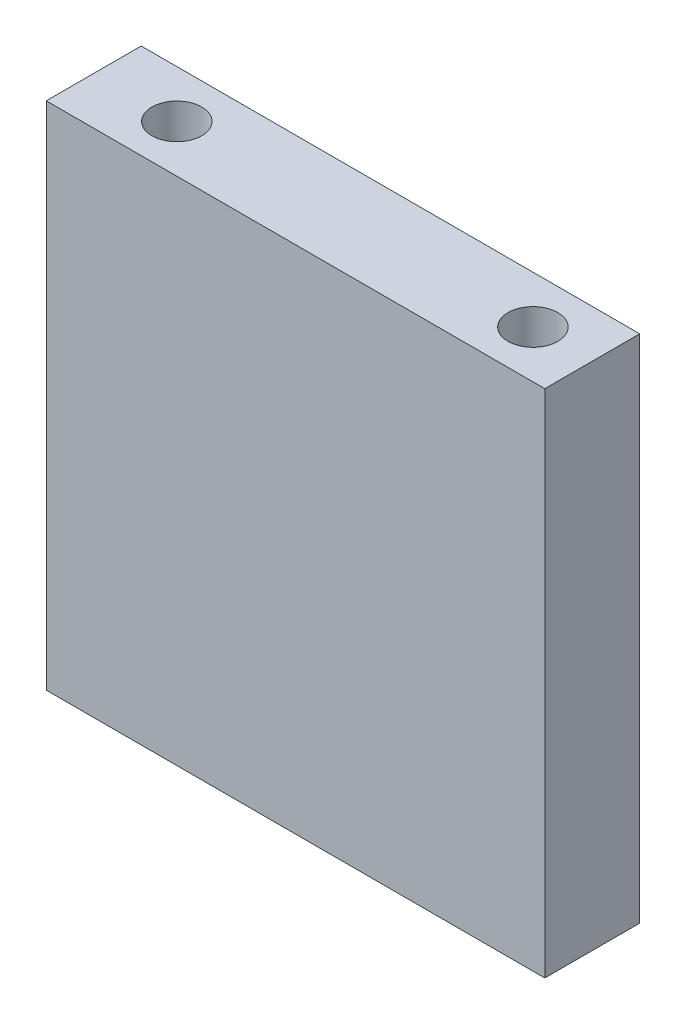
SolidWorks part; units mm, degrees
ref_plane "Front Plane" through (0, 0, 0) normal (0, 0, 1) x (1, 0, 0)
ref_plane "Top Plane" through (0, 0, 0) normal (0, 1, 0) x (1, 0, 0)
ref_plane "Right Plane" through (0, 0, 0) normal (1, 0, 0) x (0, 0, -1)
sketch "Sketch1" plane through (0, 0, 0) normal (0, 0, 1) x (1, 0, 0)
  line L1 (0, 0) -> (42, 0)
  line L2 (0, 0) -> (0, 43)
  line L3 (0, 43) -> (42, 43)
  line L4 (42, 0) -> (42, 43)
  dimension "D1" = 43
  dimension "D2" = 42
extrude "Boss-Extrude1" add sketch "Sketch1" along normal blind 8
sketch "Sketch2" plane through (0, 0, 0) normal (0, -1, 0) x (1, 0, 0)
  line L2 (42, 8) -> (42, 0) construction
  line L3 (42, 4) -> (37, 4)
  circle A0 centre (37, 4) radius 2.1
  circle A1 centre (7, 4) radius 2.1
extrude "Cut-Extrude1" cut sketch "Sketch2" against normal blind 10
sketch "Sketch3" plane through (0, 43, 0) normal (0, 1, 0) x (1, 0, 0)
  circle A0 centre (37, -4) radius 2.1
  circle A1 centre (7, -4) radius 2.1
extrude "Cut-Extrude2" cut sketch "Sketch3" against normal blind 10
